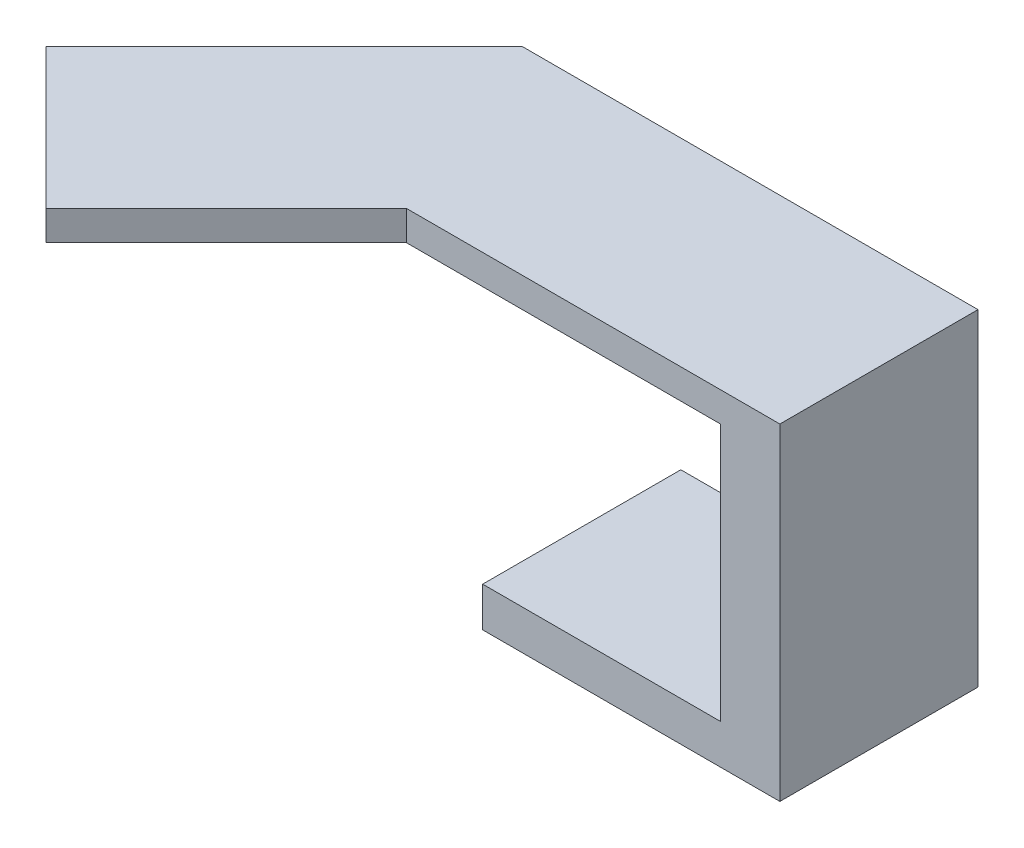
SolidWorks part; units mm, degrees
ref_plane "Front Plane" through (0, 0, 0) normal (0, 0, 1) x (1, 0, 0)
ref_plane "Top Plane" through (0, 0, 0) normal (0, 1, 0) x (1, 0, 0)
ref_plane "Right Plane" through (0, 0, 0) normal (1, 0, 0) x (0, 0, -1)
sketch "Sketch1" plane through (0, 0, 0) normal (0, 1, 0) x (1, 0, 0)
  line L0 (-10.2532, 4.4579) -> (-22.274, -7.5629)
  line L1 (-6.111, -5.5421) -> (12.7468, -5.5421)
  line L3 (-10.2532, 4.4579) -> (12.7468, 4.4579)
  line L4 (12.7468, -5.5421) -> (12.7468, 4.4579)
  line L5 (-8.3603, -2.9238) -> (12.7468, 4.4579) construction
  line L6 (-10.2532, 4.4579) -> (12.7468, -5.5421) construction
  line L7 (-22.274, -7.5629) -> (-15.2029, -14.634)
  line L8 (-15.2029, -14.634) -> (-6.111, -5.5421)
  point P0 (0, 0)
  dimension "D1" = 10
  dimension "D2" = 23
  dimension "D3" = 135
  dimension "D4" = 17
  dimension "D5" = 10
extrude "Boss-Extrude1" add sketch "Sketch1" along normal blind 1.5
sketch "Sketch2" plane through (0, 0, 0) normal (0, -1, 0) x (1, 0, 0)
  line L0 (12.7468, -4.4579) -> (-10.2532, -4.4579) construction
  line L1 (12.7468, 5.5421) -> (9.7468, 5.5421)
  line L2 (12.7468, 5.5421) -> (12.7468, -4.4579)
  line L3 (12.7468, -4.4579) -> (9.7468, -4.4579)
  line L4 (9.7468, 5.5421) -> (9.7468, -4.4579)
  dimension "D1" = 3
extrude "Boss-Extrude2" add sketch "Sketch2" along normal blind 15
sketch "Sketch3" plane through (9.7468, 0, 0) normal (-1, 0, 0) x (0, 0, 1)
  line L0 (5.5421, -15) -> (5.5421, 0) construction
  line L1 (-4.4579, -15) -> (5.5421, -15)
  line L2 (-4.4579, -15) -> (-4.4579, -13)
  line L3 (-4.4579, -13) -> (5.5421, -13)
  line L4 (5.5421, -15) -> (5.5421, -13)
  dimension "D1" = 2
extrude "Boss-Extrude3" add sketch "Sketch3" along normal blind 12
